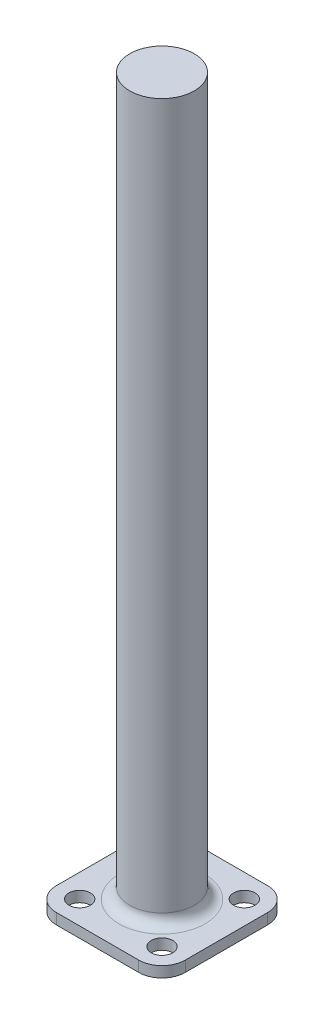
SolidWorks part; units mm, degrees
ref_plane "Front Plane" through (0, 0, 0) normal (0, 0, 1) x (1, 0, 0)
ref_plane "Top Plane" through (0, 0, 0) normal (0, 1, 0) x (1, 0, 0)
ref_plane "Right Plane" through (0, 0, 0) normal (1, 0, 0) x (0, 0, -1)
sketch "Sketch1" plane through (0, 0, 0) normal (0, 1, 0) x (1, 0, 0)
  line L1 (-5.75, 5.75) -> (5.75, 5.75)
  line L2 (-5.75, 5.75) -> (-5.75, -5.75)
  line L3 (-5.75, -5.75) -> (5.75, -5.75)
  line L4 (5.75, 5.75) -> (5.75, -5.75)
  line L5 (0, -5.75) -> (0, 5.75) construction
  line L6 (-5.75, 0) -> (0, 0) construction
  line L7 (-9, 9) -> (9, 9)
  line L8 (-9, 9) -> (-9, -9)
  line L9 (-9, -9) -> (9, -9)
  line L10 (9, 9) -> (9, -9)
  line L11 (0, -9) -> (0, 9) construction
  line L12 (-9, 0) -> (0, 0) construction
  circle A0 centre (-5.75, 5.75) radius 1.5
  circle A1 centre (5.75, 5.75) radius 1.5
  circle A2 centre (5.75, -5.75) radius 1.5
  circle A3 centre (-5.75, -5.75) radius 1.5
  arc A4 (-5.75, 9) -> (-9, 5.75) centre (-5.75, 5.75) ccw
  arc A5 (9, 5.75) -> (5.75, 9) centre (5.75, 5.75) ccw
  arc A6 (5.75, -9) -> (9, -5.75) centre (5.75, -5.75) ccw
  arc A7 (-9, -5.75) -> (-5.75, -9) centre (-5.75, -5.75) ccw
  point P0 (0, 0)
  point P11 (0, 0)
  dimension "D2" = 18
  dimension "D1" = 11.5
extrude "Boss-Extrude1" add sketch "Sketch1" along normal blind 1.5 contours L8 A7 L9 A6 L10 A5 L7 A4 A3 L2 A0 L1 A1 L4 A2 L3 | A3 L3 A2 L4 A1 L1 A0 L2
sketch "Sketch2" plane through (0, 1.5, 0) normal (0, 1, 0) x (1, 0, 0)
  circle A0 centre (0, 0) radius 4.5
sketch "Sketch3" plane through (-9, 0, 0) normal (-1, 0, 0) x (0, 0, 1)
  line L0 (0, 0) -> (0.4019, 1.5)
  line L1 (-5.75, 0) -> (5.75, 0) construction
  line L2 (-5.75, 1.5) -> (5.75, 1.5) construction
  line L3 (0.4019, 1.5) -> (1.919, 1.5)
  dimension "D1" = 105
extrude "Boss-Extrude2" add sketch "Sketch2" along normal blind 100
sketch "Sketch4" plane through (0, 101.5, 0) normal (0, 1, 0) x (1, 0, 0)
  circle A0 centre (0, -25.8819) radius 7.5
extrude "Boss-Extrude3" [suppressed] add sketch "Sketch4" along normal blind 1
fillet "Fillet1" [suppressed] radius 2
fillet "Fillet2" radius 1.5 1 edges at (0, 1.5, 4.5)
